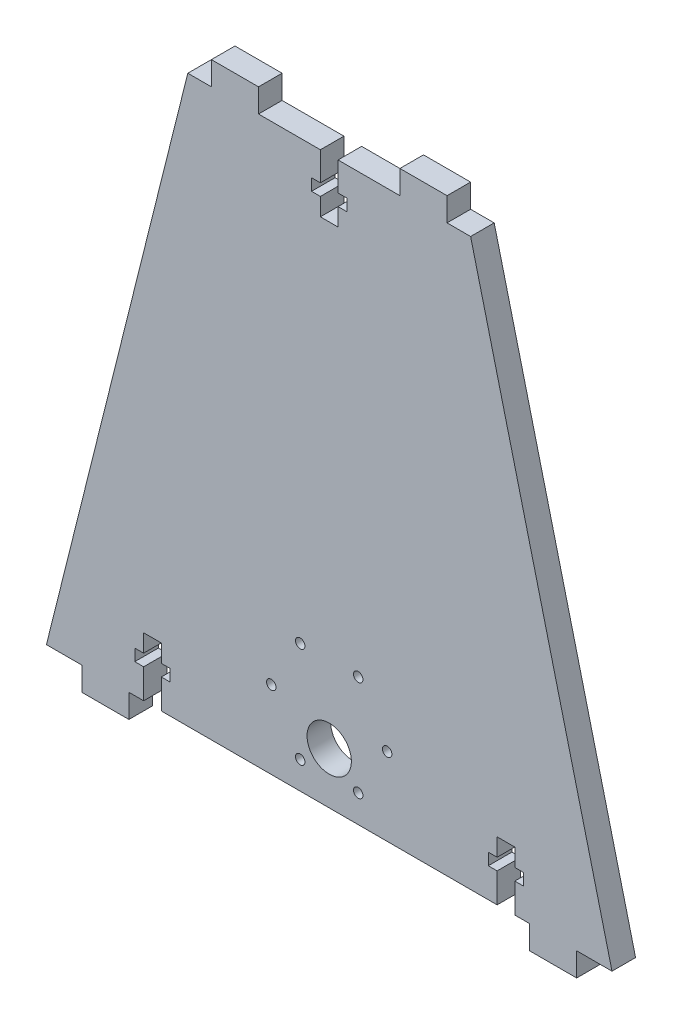
SolidWorks part; units mm, degrees
ref_plane "Front Plane" through (0, 0, 0) normal (0, 0, 1) x (1, 0, 0)
ref_plane "Top Plane" through (0, 0, 0) normal (0, 1, 0) x (1, 0, 0)
ref_plane "Right Plane" through (0, 0, 0) normal (1, 0, 0) x (0, 0, -1)
sketch "Sketch2" plane through (0, 0, 0) normal (0, 0, 1) x (1, 0, 0)
  line L0 (0, 0) -> (-9.525, 0)
  line L1 (-152.4, 0) -> (-114.3, 152.4)
  line L2 (-95.25, 152.4) -> (-78.5812, 152.4)
  line L3 (-38.1, 152.4) -> (0, 0)
  line L4 (-30.9562, 0) -> (-121.4438, 0)
  line L5 (-22.225, 0) -> (-26.1937, 0)
  line L6 (-107.95, 152.4) -> (-114.3, 152.4)
  line L7 (-126.2062, 0) -> (-130.175, 0)
  line L8 (-130.175, 0) -> (-130.175, -6.35)
  line L9 (-130.175, -6.35) -> (-142.875, -6.35)
  line L10 (-142.875, 0) -> (-142.875, -6.35)
  line L11 (-73.8187, 152.4) -> (-73.8187, 144.6852)
  line L12 (-71.4375, 141.5102) -> (-73.8187, 141.5102)
  line L13 (-126.2062, 0) -> (-126.2062, 7.9375)
  line L14 (-126.2062, 15.875) -> (-121.4437, 15.875)
  line L15 (-121.4438, 0) -> (-121.4438, 7.9375)
  line L16 (-128.5875, 11.1125) -> (-126.2062, 11.1125)
  line L17 (-71.4375, 144.6852) -> (-73.8187, 144.6852)
  line L18 (-128.5875, 7.9375) -> (-126.2062, 7.9375)
  line L19 (-119.0625, 11.1125) -> (-119.0625, 7.9375)
  line L20 (-128.5875, 11.1125) -> (-128.5875, 7.9375)
  line L21 (-142.875, 0) -> (-152.4, 0)
  line L22 (-71.4375, 141.5102) -> (-71.4375, 144.6852)
  line L23 (-121.4438, 7.9375) -> (-119.0625, 7.9375)
  line L24 (-121.4437, 11.1125) -> (-119.0625, 11.1125)
  line L25 (-121.4437, 11.1125) -> (-121.4437, 15.875)
  line L26 (-126.2062, 11.1125) -> (-126.2062, 15.875)
  line L27 (-73.8187, 141.5102) -> (-73.8187, 136.7477)
  line L28 (-57.15, 152.4) -> (-57.15, 158.75)
  line L29 (-107.95, 152.4) -> (-107.95, 158.75)
  line L30 (-107.95, 158.75) -> (-95.25, 158.75)
  line L31 (-95.25, 152.4) -> (-95.25, 158.75)
  line L32 (-44.45, 158.75) -> (-57.15, 158.75)
  line L33 (-44.45, 152.4) -> (-44.45, 158.75)
  line L34 (-26.1937, 11.1125) -> (-26.1937, 15.875)
  line L35 (-30.9562, 11.1125) -> (-30.9562, 15.875)
  line L36 (-30.9562, 11.1125) -> (-33.3375, 11.1125)
  line L37 (-30.9562, 7.9375) -> (-33.3375, 7.9375)
  line L39 (-23.8125, 11.1125) -> (-23.8125, 7.9375)
  line L40 (-33.3375, 11.1125) -> (-33.3375, 7.9375)
  line L41 (-23.8125, 7.9375) -> (-26.1937, 7.9375)
  line L42 (-78.5813, 141.5102) -> (-78.5813, 136.7477)
  line L43 (-23.8125, 11.1125) -> (-26.1937, 11.1125)
  line L44 (-30.9562, 0) -> (-30.9562, 7.9375)
  line L45 (-26.1937, 15.875) -> (-30.9562, 15.875)
  line L46 (-80.9625, 141.5102) -> (-80.9625, 144.6852)
  line L47 (-26.1937, 0) -> (-26.1937, 7.9375)
  line L48 (-80.9625, 144.6852) -> (-78.5812, 144.6852)
  line L49 (-80.9625, 141.5102) -> (-78.5813, 141.5102)
  line L51 (-78.5813, 136.7477) -> (-73.8187, 136.7477)
  line L52 (-78.5812, 152.4) -> (-78.5812, 144.6852)
  line L53 (-9.525, 0) -> (-9.525, -6.35)
  line L54 (-22.225, -6.35) -> (-9.525, -6.35)
  line L55 (-22.225, 0) -> (-22.225, -6.35)
  line L59 (-44.45, 152.4) -> (-38.1, 152.4)
  line L60 (-73.8187, 152.4) -> (-57.15, 152.4)
  dimension "D1" = 152.4
  dimension "D2" = 152.4
  dimension "D3" = 76.2
  dimension "D4" = 6.35
  dimension "D5" = 38.1
  dimension "D6" = 12.7
  dimension "D8" = 6.35
  dimension "D9" = 4.7625
  dimension "D10" = 3.175
  dimension "D11" = 9.525
  dimension "D12" = 15.875
  dimension "D13" = 7.9375
  dimension "D14" = 12.7
extrude "Boss-Extrude1" add sketch "Sketch2" along normal blind 6.35 contours L3 L0 L53 L54 L55 L5 L47 L41 L39 L43 L34 L45 L35 L36 L40 L37 L44 L4 L15 L23 L19 L24 L25 L14 L26 L16 L20 L18 L13 L7 L8 L9 L10 L21 L1 L6 L29 L30 L31 L2 L52 L48 L46 L49 L42 L51 L27 L12 L22 L17 L11 L60 L28 L32 L33 L59
sketch "Sketch4" plane through (0, 0, 0) normal (0, 0, -1) x (-1, 0, 0)
  circle A1 centre (76.2, 13.843) radius 5.969
  circle A2 centre (68.3895, 34.4832) radius 1.27
  circle A3 centre (84.0105, 34.4832) radius 1.27
  circle A4 centre (91.821, 20.955) radius 1.27
  circle A5 centre (84.0105, 7.4268) radius 1.27
  circle A6 centre (68.3895, 7.4268) radius 1.27
  circle A7 centre (60.579, 20.955) radius 1.27
  point P8 (76.2, 2.54)
  point P11 (76.2, 7.874)
  point P15 (67.7545, 35.583)
  point P29 (76.2, 20.955)
  dimension "D4" = 11.938
  dimension "D6" = 2.54
  dimension "D3" = 5.334
extrude "Cut-Extrude3" cut sketch "Sketch4" against normal blind 6.35
